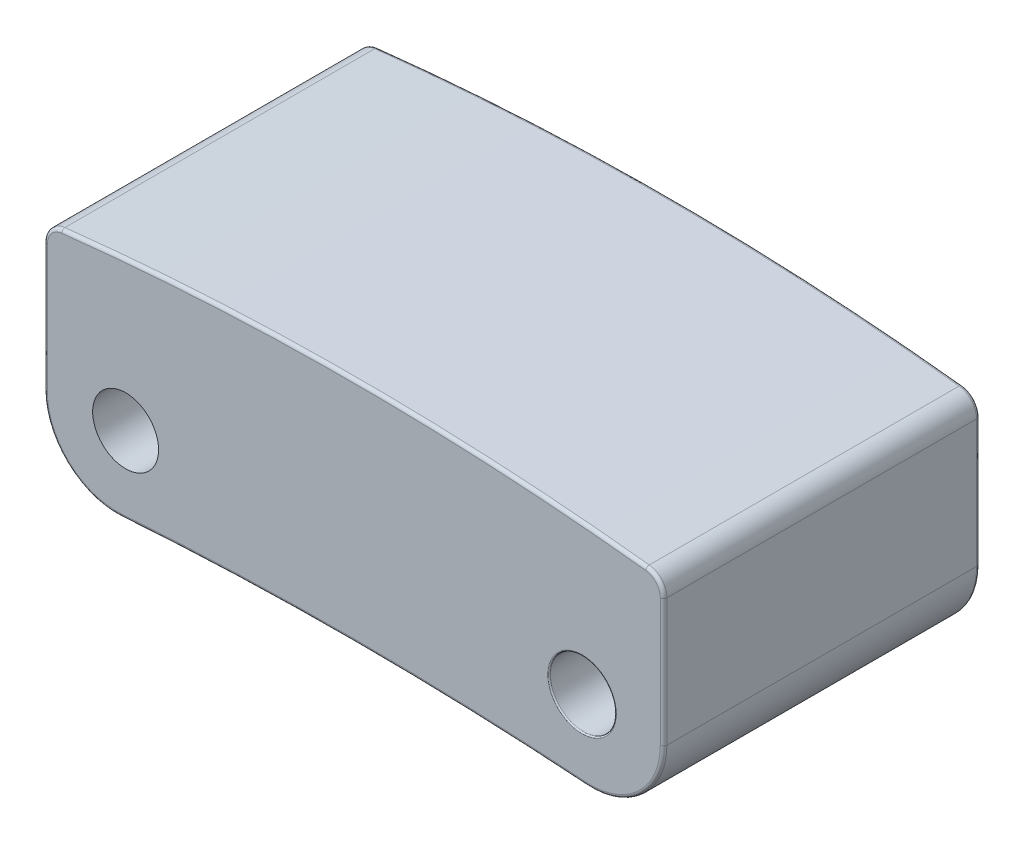
SolidWorks part; units mm, degrees
ref_plane "Front Plane" through (0, 0, 0) normal (0, 0, 1) x (1, 0, 0)
ref_plane "Top Plane" through (0, 0, 0) normal (0, 1, 0) x (1, 0, 0)
ref_plane "Right Plane" through (0, 0, 0) normal (1, 0, 0) x (0, 0, -1)
sketch "Sketch1" plane through (0, 0, 0) normal (0, 0, 1) x (1, 0, 0)
  line L0 (55, 0) -> (-55, 0) construction
  line L1 (-4.7, 1.85) -> (4.7, 1.85)
  line L2 (-4.7, 1.85) -> (-4.7, -1.85)
  line L3 (-4.7, -1.85) -> (4.7, -1.85)
  line L4 (4.7, 1.85) -> (4.7, -1.85)
  line L5 (0, -55) -> (0, 55) construction
  dimension "D1" = 9.4
  dimension "D2" = 3.7
  dimension "D3" = 1.85
  dimension "D4" = 4.7
extrude "Boss-Extrude1" add sketch "Sketch1" along normal mid plane 4.8
sketch "Sketch2" plane through (0, 0, 2.4) normal (0, 0, 1) x (1, 0, 0)
  line L0 (-4.7, 1.85) -> (-4.7, -1.85) construction
  line L1 (4.7, -1.85) -> (4.7, 1.85) construction
  line L2 (-4.7, -1.85) -> (4.7, -1.85) construction
  line L3 (4.7, 1.85) -> (-4.7, 1.85) construction
  line L4 (-4.7, 1.55) -> (-7.1207, 4.0114)
  line L5 (-7.1207, 4.0114) -> (5.5359, 3.8867)
  line L6 (5.5359, 3.8867) -> (4.7, 1.55)
  line L7 (4.7, -1.85) -> (0.3506, -3.782)
  line L8 (-4.7, -1.85) -> (0.3506, -3.782)
  arc A0 (-4.7, 1.55) -> (4.7, 1.55) centre (0, -38.1729) cw
  arc A1 (-4.7, -1.85) -> (4.7, -1.85) centre (0, -51.6286) cw
  dimension "D4" = 40
  dimension "D5" = 50
  dimension "D1" = 0
  dimension "D2" = 0.3
  dimension "D3" = 0.3
extrude "Cut-Extrude1" cut sketch "Sketch2" against normal blind 4.8
fillet "Fillet1" radius 1.1 2 edges at (4.7, -1.85, 0) (-4.7, -1.85, 0)
fillet "Fillet2" radius 0.3 2 edges at (4.7, 1.55, 0) (-4.7, 1.55, 0)
fillet "Fillet3" radius 0.05 16 edges at (-4.6236, 1.4825, -2.4) (-4.7, 0.3135, -2.4) (-4.3499, -1.4603, -2.4) (0, -1.6286, -2.4) (4.3499, -1.4603, -2.4) (4.7, 0.3135, -2.4) (4.6236, 1.4825, -2.4) (0, 1.8271, -2.4) (4.3499, -1.4603, 2.4) (0, -1.6286, 2.4) (-4.3499, -1.4603, 2.4) (-4.7, 0.3135, 2.4) (-4.6236, 1.4825, 2.4) (0, 1.8271, 2.4) (4.6236, 1.4825, 2.4) (4.7, 0.3135, 2.4)
sketch "Sketch3" plane through (0, 0, 2.4) normal (0, 0, 1) x (1, 0, 0)
  circle A0 centre (3.4626, -0.5787) radius 0.5
  dimension "D1" = 1
extrude "Cut-Extrude2" cut sketch "Sketch3" against normal blind 4.8
fillet "Fillet4" radius 0.02 2 edges at (3.9626, -0.5787, -2.4) (3.9626, -0.5787, 2.4)
mirror "Mirror1" about plane through (0, 0, 0) normal (1, 0, 0) of "Cut-Extrude2"
sketch "Sketch4" plane through (0, 0, 2.4) normal (0, 0, 1) x (1, 0, 0)
  line L1 (-4.2939, 0) -> (-2.4123, 0)
  line L2 (-4.2939, 0) -> (-4.2939, -1.1776)
  line L3 (-4.2939, -1.1776) -> (-2.4123, -1.1776)
  line L4 (-2.4123, 0) -> (-2.4123, -1.1776)
extrude "Boss-Extrude2" add sketch "Sketch4" against normal blind 1
sketch "Sketch5" plane through (0, 0, 1.4) normal (0, 0, -1) x (-1, 0, 0)
  circle A1 centre (3.4626, -0.5787) radius 0.5
  circle A2 centre (3.4626, -0.5787) radius 0.5
  dimension "D1" = 0
extrude "Cut-Extrude3" cut sketch "Sketch5" against normal blind 10
sketch "Sketch6" plane through (0, 0, -2.4) normal (0, 0, -1) x (-1, 0, 0)
  circle A0 centre (3.5267, -0.6079) radius 0.7375
extrude "Boss-Extrude3" add sketch "Sketch6" against normal blind 1
sketch "Sketch7" plane through (0, 0, 0) normal (0, 1, 0) x (1, 0, 0)
  line L0 (-3.526, -2.4) -> (3.526, -2.4) construction
  line L1 (-4.7, 2.35) -> (-4.7, -2.35) construction
  circle A0 centre (-0.7, -0.9) radius 0.4
  dimension "D1" = 0.8
  dimension "D2" = 1.5
  dimension "D3" = 4
extrude "Cut-Extrude4" cut sketch "Sketch7" along normal offset from surface (8.7665 mm away) 0.4 from offset 10 offset against normal yes
fillet "Fillet5" radius 0.05 1 edges at (-0.792, -1.6349, 1.2893)
